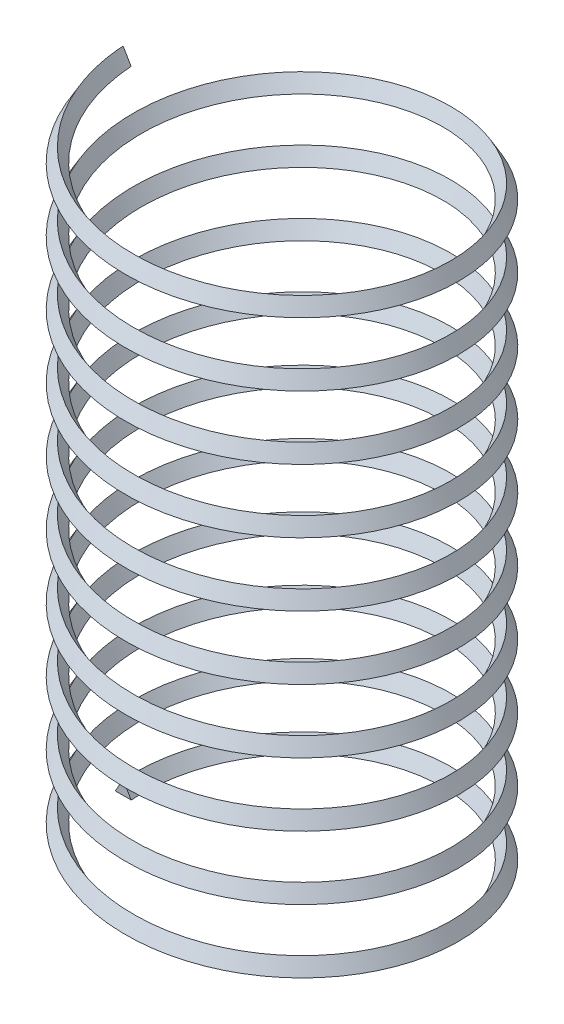
SolidWorks part; units mm, degrees
ref_plane "Front Plane" through (0, 0, 0) normal (0, 0, 1) x (1, 0, 0)
ref_plane "Top Plane" through (0, 0, 0) normal (0, 1, 0) x (1, 0, 0)
ref_plane "Right Plane" through (0, 0, 0) normal (1, 0, 0) x (0, 0, -1)
sketch "Sketch2" plane through (0, 0, 0) normal (0, 1, 0) x (1, 0, 0)
  circle A0 centre (0, 0) radius 50
  dimension "D1" = 100
curve "Helix/Spiral1" pitch 20 height 200 turns 10
ref_plane "Plane1" through (0, 0, 0) normal (0, 0, 1) x (1, 0, 0)
sketch "Sketch3" plane through (0, 0, 0) normal (0, 0, 1) x (1, 0, 0)
  line L0 (-50.0081, 2.8867) -> (-47.496, -1.4364)
  line L1 (-47.496, -1.4364) -> (-52.496, -1.4504)
  line L2 (-52.496, -1.4504) -> (-50.0081, 2.8867)
  line L3 (-50.0081, 2.8867) -> (-49.996, -1.4434) construction
  line L6 (-48.752, 0.7252) -> (-52.496, -1.4504) construction
  spline S0 degree 3 poles (-50, 0) (-50, 0.2126) (-49.3261, 0.6391) (-46.3343, 1.2779) (-41.4816, 1.9169) (-34.9629, 2.5559) (-27.0401, 3.1949) (-18.0313, 3.8339) (-8.2983, 4.4728) (1.768, 5.1118) (11.7632, 5.7508) (21.286, 6.3898) (29.954, 7.0288) (37.4189, 7.6677) (43.381, 8.3067) (47.6009, 8.9457) (49.909, 9.5847) (50.2127, 10.2236) (48.4998, 10.8626) (44.8391, 11.5016) (39.3775, 12.1406) (32.3345, 12.7796) (23.9928, 13.4185) (14.6876, 14.0575) (4.7925, 14.6965) (-5.2951, 15.3355) (-15.1701, 15.9744) (-24.4357, 16.6134) (-32.72, 17.2524) (-39.6902, 17.8914) (-45.0664, 18.5304) (-48.6326, 19.1693) (-50.2457, 19.8083) (-49.8408, 20.4473) (-47.4342, 21.0863) (-43.1226, 21.7252) (-37.0791, 22.3642) (-29.5464, 23.0032) (-20.8271, 23.6422) (-11.2714, 24.2812) (-1.263, 24.9201) (8.7962, 25.5591) (18.5021, 26.1981) (27.4649, 26.8371) (35.3246, 27.476) (41.7657, 28.115) (46.5294, 28.754) (49.4244, 29.393) (50.3344, 30.0319) (49.2229, 30.6709) (46.1345, 31.3099) (41.1933, 31.9489) (34.5977, 32.5879) (26.6126, 33.2268) (17.5587, 33.8658) (7.7996, 34.5048) (-2.2728, 35.1438) (-12.2538, 35.7827) (-21.7428, 36.4217) (-30.3585, 37.0607) (-37.755, 37.6997) (-43.6351, 38.3387) (-47.7628, 38.9776) (-49.9723, 39.6166) (-50.1747, 40.2556) (-48.3621, 40.8946) (-44.6072, 41.5335) (-39.0608, 42.1725) (-31.9456, 42.8115) (-23.5475, 43.4505) (-14.2036, 44.0895) (-4.2893, 44.7284) (5.7973, 45.3674) (15.651, 46.0064) (24.8762, 46.6454) (33.1023, 47.2843) (39.999, 47.9233) (45.2892, 48.5623) (48.7605, 49.2013) (50.2736, 49.8403) (49.7675, 50.4792) (47.2627, 51.1182) (42.8598, 51.7572) (36.7355, 52.3962) (29.1359, 53.0351) (20.3661, 53.6741) (10.7784, 54.3131) (0.7578, 54.9521) (-9.2932, 55.5911) (-18.971, 56.23) (-27.8869, 56.869) (-35.6828, 57.508) (-42.0456, 58.147) (-46.7198, 58.7859) (-49.5177, 59.4249) (-50.3268, 60.0639) (-49.1147, 60.7029) (-45.9301, 61.3419) (-40.9009, 61.9808) (-34.229, 62.6198) (-26.1824, 63.2588) (-17.0843, 63.8978) (-7.3001, 64.5367) (2.7774, 65.1757) (12.7433, 65.8147) (22.1974, 66.4537) (30.76, 67.0927) (38.0872, 67.7316) (43.8848, 68.3706) (47.9199, 69.0096) (50.0304, 69.6486) (50.1317, 70.2875) (48.2196, 70.9265) (44.3709, 71.5655) (38.7402, 72.2045) (31.5536, 72.8435) (23.0997, 73.4824) (13.7182, 74.1214) (3.7857, 74.7604) (-6.2989, 75.3994) (-16.1304, 76.0383) (-25.3142, 76.6773) (-33.4813, 77.3163) (-40.3037, 77.9553) (-45.5074, 78.5942) (-48.8835, 79.2332) (-50.2964, 79.8722) (-49.6892, 80.5112) (-47.0865, 81.1502) (-42.5927, 81.7891) (-36.3883, 82.4281) (-28.7224, 83.0671) (-19.9031, 83.7061) (-10.2844, 84.345) (-0.2526, 84.984) (9.7893, 85.623) (19.438, 86.262) (28.3061, 86.901) (36.0373, 87.5399) (42.3213, 88.1789) (46.9055, 88.8179) (49.6059, 89.4569) (50.3141, 90.0958) (49.0016, 90.7348) (45.7211, 91.3738) (40.6043, 92.0128) (33.8568, 92.6518) (25.7496, 93.2907) (16.6082, 93.9297) (6.7998, 94.5687) (-3.2817, 95.2077) (-13.2314, 95.8466) (-22.6497, 96.4856) (-31.1583, 97.1246) (-38.4156, 97.7636) (-44.1301, 98.4026) (-48.0722, 99.0415) (-50.0836, 99.6805) (-50.0836, 100.3195) (-48.0722, 100.9585) (-44.1301, 101.5974) (-38.4156, 102.2364) (-31.1583, 102.8754) (-22.6497, 103.5144) (-13.2314, 104.1534) (-3.2817, 104.7923) (6.7998, 105.4313) (16.6082, 106.0703) (25.7496, 106.7093) (33.8568, 107.3482) (40.6043, 107.9872) (45.7211, 108.6262) (49.0016, 109.2652) (50.3141, 109.9042) (49.6059, 110.5431) (46.9055, 111.1821) (42.3213, 111.8211) (36.0373, 112.4601) (28.3061, 113.099) (19.438, 113.738) (9.7893, 114.377) (-0.2526, 115.016) (-10.2844, 115.655) (-19.9031, 116.2939) (-28.7224, 116.9329) (-36.3883, 117.5719) (-42.5927, 118.2109) (-47.0865, 118.8498) (-49.6892, 119.4888) (-50.2964, 120.1278) (-48.8835, 120.7668) (-45.5074, 121.4058) (-40.3037, 122.0447) (-33.4813, 122.6837) (-25.3142, 123.3227) (-16.1304, 123.9617) (-6.2989, 124.6006) (3.7857, 125.2396) (13.7182, 125.8786) (23.0997, 126.5176) (31.5536, 127.1565) (38.7402, 127.7955) (44.3709, 128.4345) (48.2196, 129.0735) (50.1317, 129.7125) (50.0304, 130.3514) (47.9199, 130.9904) (43.8848, 131.6294) (38.0872, 132.2684) (30.76, 132.9073) (22.1974, 133.5463) (12.7433, 134.1853) (2.7774, 134.8243) (-7.3001, 135.4633) (-17.0843, 136.1022) (-26.1824, 136.7412) (-34.229, 137.3802) (-40.9009, 138.0192) (-45.9301, 138.6581) (-49.1147, 139.2971) (-50.3268, 139.9361) (-49.5177, 140.5751) (-46.7198, 141.2141) (-42.0456, 141.853) (-35.6828, 142.492) (-27.8869, 143.131) (-18.971, 143.77) (-9.2932, 144.4089) (0.7578, 145.0479) (10.7784, 145.6869) (20.3661, 146.3259) (29.1359, 146.9649) (36.7355, 147.6038) (42.8598, 148.2428) (47.2627, 148.8818) (49.7675, 149.5208) (50.2736, 150.1597) (48.7605, 150.7987) (45.2892, 151.4377) (39.999, 152.0767) (33.1023, 152.7157) (24.8762, 153.3546) (15.651, 153.9936) (5.7973, 154.6326) (-4.2893, 155.2716) (-14.2036, 155.9105) (-23.5475, 156.5495) (-31.9456, 157.1885) (-39.0608, 157.8275) (-44.6072, 158.4665) (-48.3621, 159.1054) (-50.1747, 159.7444) (-49.9723, 160.3834) (-47.7628, 161.0224) (-43.6351, 161.6613) (-37.755, 162.3003) (-30.3585, 162.9393) (-21.7428, 163.5783) (-12.2538, 164.2173) (-2.2728, 164.8562) (7.7996, 165.4952) (17.5587, 166.1342) (26.6126, 166.7732) (34.5977, 167.4121) (41.1933, 168.0511) (46.1345, 168.6901) (49.2229, 169.3291) (50.3344, 169.9681) (49.4244, 170.607) (46.5294, 171.246) (41.7657, 171.885) (35.3246, 172.524) (27.4649, 173.1629) (18.5021, 173.8019) (8.7962, 174.4409) (-1.263, 175.0799) (-11.2714, 175.7188) (-20.8271, 176.3578) (-29.5464, 176.9968) (-37.0791, 177.6358) (-43.1226, 178.2748) (-47.4342, 178.9137) (-49.8408, 179.5527) (-50.2457, 180.1917) (-48.6326, 180.8307) (-45.0664, 181.4696) (-39.6902, 182.1086) (-32.72, 182.7476) (-24.4357, 183.3866) (-15.1701, 184.0256) (-5.2951, 184.6645) (4.7925, 185.3035) (14.6876, 185.9425) (23.9928, 186.5815) (32.3345, 187.2204) (39.3775, 187.8594) (44.8391, 188.4984) (48.4998, 189.1374) (50.2127, 189.7764) (49.909, 190.4153) (47.6009, 191.0543) (43.381, 191.6933) (37.4189, 192.3323) (29.954, 192.9712) (21.286, 193.6102) (11.7632, 194.2492) (1.768, 194.8882) (-8.2983, 195.5272) (-18.0313, 196.1661) (-27.0401, 196.8051) (-34.9629, 197.4441) (-41.4816, 198.0831) (-46.3343, 198.7221) (-49.3261, 199.3609) (-50, 199.7874) (-50, 200) knots 0 0 0 0 0.003195 0.00639 0.009585 0.01278 0.015974 0.019169 0.022364 0.025559 0.028754 0.031949 0.035144 0.038339 0.041534 0.044728 0.047923 0.051118 0.054313 0.057508 0.060703 0.063898 0.067093 0.070288 0.073482 0.076677 0.079872 0.083067 0.086262 0.089457 0.092652 0.095847 0.099042 0.102236 0.105431 0.108626 0.111821 0.115016 0.118211 0.121406 0.124601 0.127796 0.13099 0.134185 0.13738 0.140575 0.14377 0.146965 0.15016 0.153355 0.15655 0.159744 0.162939 0.166134 0.169329 0.172524 0.175719 0.178914 0.182109 0.185304 0.188498 0.191693 0.194888 0.198083 0.201278 0.204473 0.207668 0.210863 0.214058 0.217252 0.220447 0.223642 0.226837 0.230032 0.233227 0.236422 0.239617 0.242812 0.246006 0.249201 0.252396 0.255591 0.258786 0.261981 0.265176 0.268371 0.271565 0.27476 0.277955 0.28115 0.284345 0.28754 0.290735 0.29393 0.297125 0.300319 0.303514 0.306709 0.309904 0.313099 0.316294 0.319489 0.322684 0.325879 0.329073 0.332268 0.335463 0.338658 0.341853 0.345048 0.348243 0.351438 0.354633 0.357827 0.361022 0.364217 0.367412 0.370607 0.373802 0.376997 0.380192 0.383387 0.386581 0.389776 0.392971 0.396166 0.399361 0.402556 0.405751 0.408946 0.412141 0.415335 0.41853 0.421725 0.42492 0.428115 0.43131 0.434505 0.4377 0.440895 0.444089 0.447284 0.450479 0.453674 0.456869 0.460064 0.463259 0.466454 0.469649 0.472843 0.476038 0.479233 0.482428 0.485623 0.488818 0.492013 0.495208 0.498403 0.501597 0.504792 0.507987 0.511182 0.514377 0.517572 0.520767 0.523962 0.527157 0.530351 0.533546 0.536741 0.539936 0.543131 0.546326 0.549521 0.552716 0.555911 0.559105 0.5623 0.565495 0.56869 0.571885 0.57508 0.578275 0.58147 0.584665 0.587859 0.591054 0.594249 0.597444 0.600639 0.603834 0.607029 0.610224 0.613419 0.616613 0.619808 0.623003 0.626198 0.629393 0.632588 0.635783 0.638978 0.642173 0.645367 0.648562 0.651757 0.654952 0.658147 0.661342 0.664537 0.667732 0.670927 0.674121 0.677316 0.680511 0.683706 0.686901 0.690096 0.693291 0.696486 0.699681 0.702875 0.70607 0.709265 0.71246 0.715655 0.71885 0.722045 0.72524 0.728435 0.731629 0.734824 0.738019 0.741214 0.744409 0.747604 0.750799 0.753994 0.757188 0.760383 0.763578 0.766773 0.769968 0.773163 0.776358 0.779553 0.782748 0.785942 0.789137 0.792332 0.795527 0.798722 0.801917 0.805112 0.808307 0.811502 0.814696 0.817891 0.821086 0.824281 0.827476 0.830671 0.833866 0.837061 0.840256 0.84345 0.846645 0.84984 0.853035 0.85623 0.859425 0.86262 0.865815 0.86901 0.872204 0.875399 0.878594 0.881789 0.884984 0.888179 0.891374 0.894569 0.897764 0.900958 0.904153 0.907348 0.910543 0.913738 0.916933 0.920128 0.923323 0.926518 0.929712 0.932907 0.936102 0.939297 0.942492 0.945687 0.948882 0.952077 0.955272 0.958466 0.961661 0.964856 0.968051 0.971246 0.974441 0.977636 0.980831 0.984026 0.98722 0.990415 0.99361 0.996805 1 1 1 1 construction
  point P5 (-50, 0)
  dimension "D1" = 5
sweep "Sweep1" add profiles "Sketch3" path "Helix/Spiral1"
